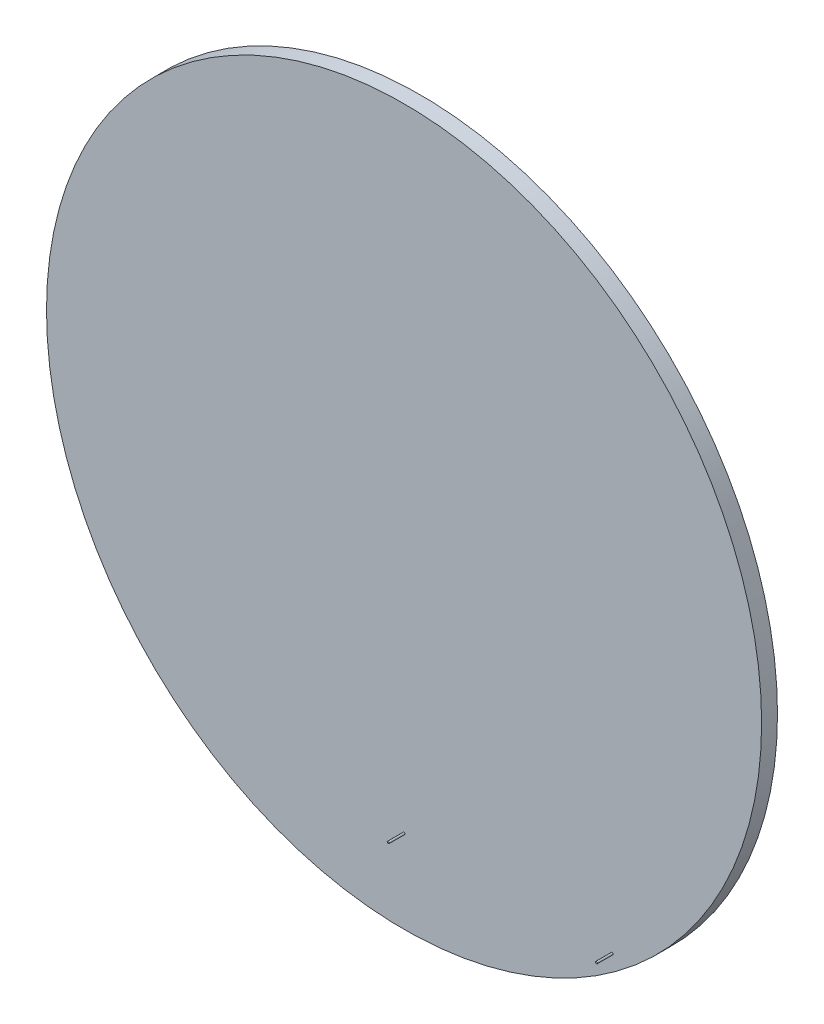
SolidWorks part; units mm, degrees
ref_plane "Front Plane" through (0, 0, 0) normal (0, 0, 1) x (1, 0, 0)
ref_plane "Top Plane" through (0, 0, 0) normal (0, 1, 0) x (1, 0, 0)
ref_plane "Right Plane" through (0, 0, 0) normal (1, 0, 0) x (0, 0, -1)
sketch "Sketch1" plane through (0, 0, 0) normal (0, 0, 1) x (1, 0, 0)
  circle A0 centre (0, 0) radius 572.6684
  dimension "D1" = 1145.3368
extrude "Boss-Extrude1" add sketch "Sketch1" along normal blind 25.4
sketch "Sketch2" plane through (0, 0, 25.4) normal (0, 0, 1) x (1, 0, 0)
  circle A0 centre (0, -439.3184) radius 1.5875
  circle A1 centre (333.375, -439.3184) radius 1.5875
  dimension "D1" = 3.175
  dimension "D2" = 3.175
  dimension "D3" = 439.3184
  dimension "D4" = 439.3184
  dimension "D5" = 333.375
extrude "Boss-Extrude2" add sketch "Sketch2" along normal blind 25.4
